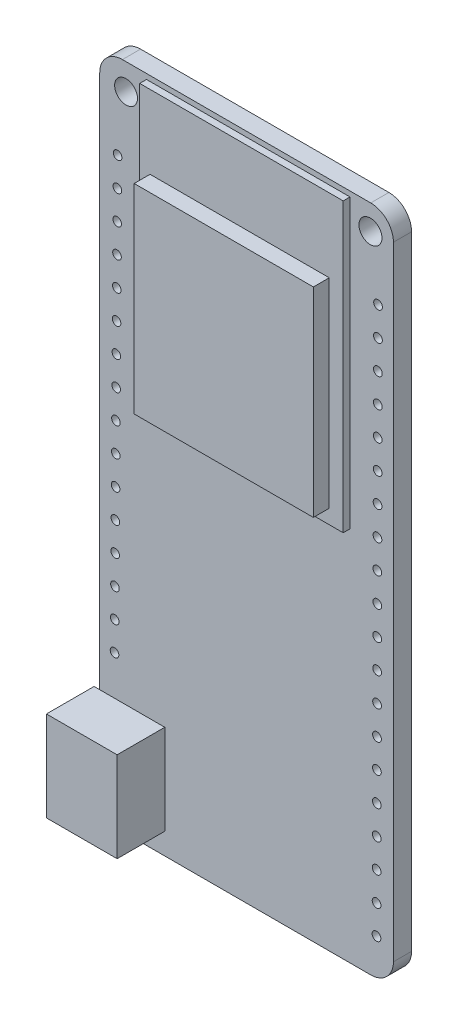
SolidWorks part; units mm, degrees
ref_plane "Plan de face" through (0, 0, 0) normal (0, 0, 1) x (1, 0, 0)
ref_plane "Plan de dessus" through (0, 0, 0) normal (0, 1, 0) x (1, 0, 0)
ref_plane "Plan de droite" through (0, 0, 0) normal (1, 0, 0) x (0, 0, -1)
sketch "Esquisse1" plane through (0, 0, 0) normal (0, 0, 1) x (1, 0, 0)
  line L0 (9.8891, 552.2662) -> (35.2891, 552.2662) construction
  line L2 (11.5316, 495.6678) -> (33.4138, 495.6678)
  line L3 (9.5316, 497.6678) -> (9.5316, 552.5859)
  line L4 (11.5316, 554.5859) -> (33.4138, 554.5859)
  line L5 (35.4138, 497.6678) -> (35.4138, 552.5859)
  line L20 (9.4954, 492.588) -> (9.4954, 547.506) [skipped]
  line L21 (9.4773, 490.048) -> (9.4773, 544.9661) [skipped]
  line L22 (9.4593, 487.5081) -> (9.4593, 542.4261) [skipped]
  line L23 (9.4412, 484.9682) -> (9.4412, 539.8862) [skipped]
  line L24 (9.4231, 482.4282) -> (9.4231, 537.3463) [skipped]
  line L25 (9.405, 479.8883) -> (9.405, 534.8063) [skipped]
  line L26 (9.3869, 477.3484) -> (9.3869, 532.2664) [skipped]
  line L27 (9.3688, 474.8084) -> (9.3688, 529.7264) [skipped]
  line L28 (9.3507, 472.2685) -> (9.3507, 527.1865) [skipped]
  line L29 (9.3326, 469.7285) -> (9.3326, 524.6466) [skipped]
  line L30 (9.3146, 467.1886) -> (9.3146, 522.1066) [skipped]
  line L31 (9.2965, 464.6487) -> (9.2965, 519.5667) [skipped]
  line L32 (9.2784, 462.1087) -> (9.2784, 517.0268) [skipped]
  line L33 (9.2603, 459.5688) -> (9.2603, 514.4868) [skipped]
  line L34 (9.5135, 495.1279) -> (9.5135, 550.0459) [skipped]
  arc A0 (33.4138, 495.6678) -> (35.4138, 497.6678) centre (33.4138, 497.6678) ccw
  arc A1 (11.5316, 495.6678) -> (9.5316, 497.6678) centre (11.5316, 497.6678) cw
  arc A2 (33.4138, 554.5859) -> (35.4138, 552.5859) centre (33.4138, 552.5859) cw
  arc A3 (9.5316, 552.5859) -> (11.5316, 554.5859) centre (11.5316, 552.5859) cw
  circle A4 centre (11.8519, 552.2815) radius 1.0078
  circle A5 centre (33.3883, 552.4005) radius 1.015
  circle A6 centre (11.1063, 547.0741) radius 0.3791
  circle A7 centre (11.0883, 544.5342) radius 0.3791
  circle A8 centre (11.0702, 541.9943) radius 0.3791
  circle A9 centre (11.0521, 539.4543) radius 0.3791
  circle A10 centre (11.034, 536.9144) radius 0.3791
  circle A11 centre (11.0159, 534.3745) radius 0.3791
  circle A12 centre (10.9978, 531.8345) radius 0.3791
  circle A13 centre (10.9797, 529.2946) radius 0.3791
  circle A14 centre (10.9616, 526.7547) radius 0.3791
  circle A15 centre (10.9436, 524.2147) radius 0.3791
  circle A16 centre (10.9255, 521.6748) radius 0.3791
  circle A17 centre (10.9074, 519.1349) radius 0.3791
  circle A18 centre (10.8893, 516.5949) radius 0.3791
  circle A19 centre (10.8712, 514.055) radius 0.3791
  circle A20 centre (10.8531, 511.515) radius 0.3791
  circle A21 centre (10.835, 508.9751) radius 0.3791
  circle A22 centre (34.0582, 547.1387) radius 0.3848
  circle A23 centre (34.0511, 544.5987) radius 0.3848
  circle A24 centre (34.0439, 542.0587) radius 0.3848
  circle A25 centre (34.0367, 539.5187) radius 0.3848
  circle A26 centre (34.0296, 536.9787) radius 0.3848
  circle A27 centre (34.0224, 534.4387) radius 0.3848
  circle A28 centre (34.0153, 531.8987) radius 0.3848
  circle A29 centre (34.0081, 529.3587) radius 0.3848
  circle A30 centre (34.0009, 526.8187) radius 0.3848
  circle A31 centre (33.9938, 524.2787) radius 0.3848
  circle A32 centre (33.9866, 521.7388) radius 0.3848
  circle A33 centre (33.9795, 519.1988) radius 0.3848
  circle A34 centre (33.9723, 516.6588) radius 0.3848
  circle A35 centre (33.9652, 514.1188) radius 0.3848
  circle A36 centre (33.958, 511.5788) radius 0.3848
  circle A37 centre (33.9508, 509.0388) radius 0.3848
  circle A38 centre (33.9437, 506.4988) radius 0.3848
  circle A39 centre (33.9365, 503.9588) radius 0.3848
  circle A40 centre (33.9294, 501.4188) radius 0.3848
  circle A41 centre (33.9222, 498.8788) radius 0.3848
  circle A43 centre (33.915, 496.3389) radius 0.3848 [skipped]
  point P14 (0, 0)
  dimension "D2" = 2
  dimension "D1" = 25.4
  dimension "D3" = 16
  dimension "D4" = 21
sketch "Esquisse2" plane through (0, 0, 0) normal (0, 0, 1) x (1, 0, 0)
  line L1 (13.653, 528.7993) -> (31.5864, 528.7993)
  line L2 (13.653, 528.7993) -> (13.653, 554.1288)
  line L3 (13.653, 554.1288) -> (31.5864, 554.1288)
  line L4 (31.5864, 528.7993) -> (31.5864, 554.1288)
sketch "Esquisse3" plane through (0, 0, 0) normal (0, 0, 1) x (1, 0, 0)
  line L1 (14.5668, 530.0558) -> (30.3585, 530.0558)
  line L2 (14.5668, 530.0558) -> (14.5668, 547.6465)
  line L3 (14.5668, 547.6465) -> (30.3585, 547.6465)
  line L4 (30.3585, 530.0558) -> (30.3585, 547.6465)
extrude "Boss.-Extru.1" add sketch "Esquisse3" along normal blind 2
extrude "Boss.-Extru.2" add sketch "Esquisse2" along normal blind 0.6
sketch "Esquisse4" plane through (0, 0, 0) normal (0, 0, 1) x (1, 0, 0)
  line L1 (15.265, 505.4941) -> (9.0339, 505.4941)
  line L2 (15.265, 505.4941) -> (15.265, 497.5598)
  line L3 (15.265, 497.5598) -> (9.0339, 497.5598)
  line L4 (9.0339, 505.4941) -> (9.0339, 497.5598)
extrude "Boss.-Extru.3" add sketch "Esquisse4" along normal blind 4.2 separate body
sketch "Esquisse5" plane through (9.0339, 0, 0) normal (-1, 0, 0) x (0, 0, 1)
  line L1 (3.6368, 504.8805) -> (0.5139, 504.8805)
  line L2 (3.6368, 504.8805) -> (3.6368, 498.1928)
  line L3 (3.6368, 498.1928) -> (0.5139, 498.1928)
  line L4 (0.5139, 504.8805) -> (0.5139, 498.1928)
extrude "Enlèv. mat.-Extru.1" cut sketch "Esquisse5" against normal blind 4.2
extrude "Boss.-Extru.5" add sketch "Esquisse1" against normal blind 1.6
